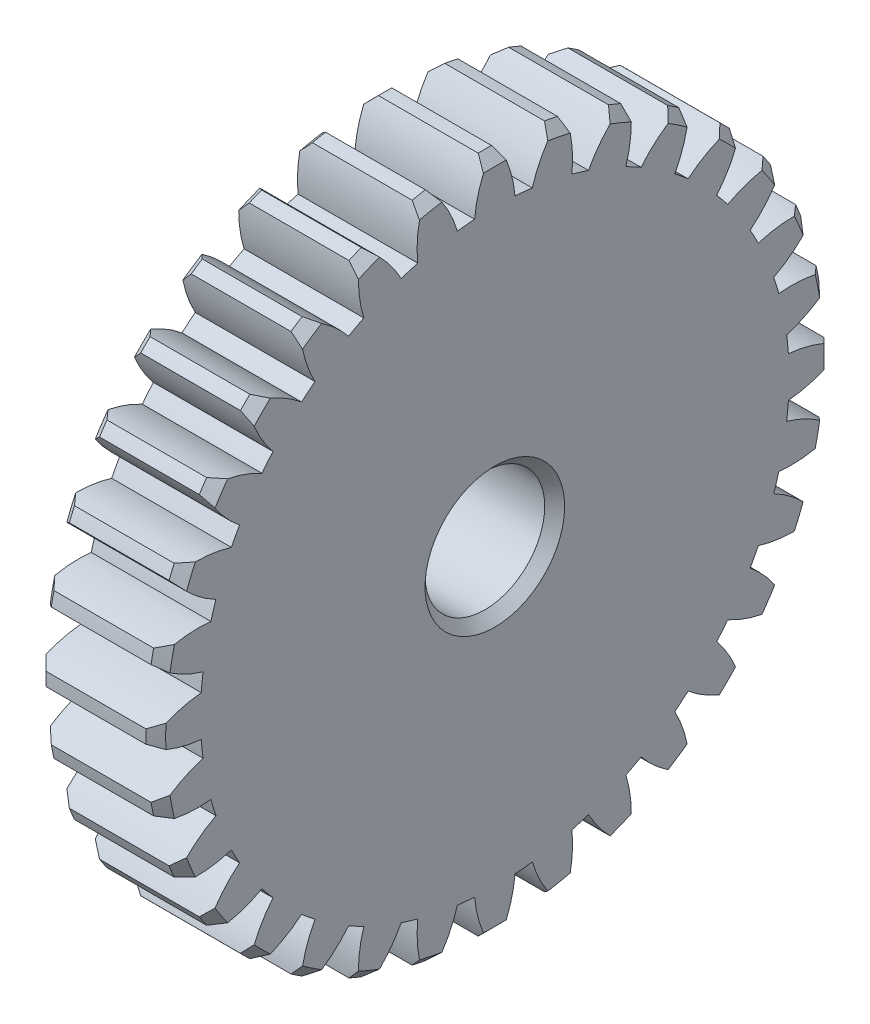
SolidWorks part; units mm, degrees
ref_plane "Front Plane" through (0, 0, 0) normal (0, 0, 1) x (1, 0, 0)
ref_plane "Top Plane" through (0, 0, 0) normal (0, 1, 0) x (1, 0, 0)
ref_plane "Right Plane" through (0, 0, 0) normal (1, 0, 0) x (0, 0, -1)
sketch "Sketch1" plane through (0, 0, 0) normal (0, 0, 1) x (1, 0, 0)
  line L0 (0, 17) -> (0, 0)
  line L1 (0, 0) -> (6, 0)
  line L2 (6, 0) -> (6, 17)
  line L3 (6, 17) -> (0, 17)
  line L4 (0, 0) -> (6, 0) construction
revolve "Revolve1" add sketch "Sketch1" angle 360 about L4
sketch "Sketch2" plane through (6, 0, 0) normal (1, 0, 0) x (0, 0, -1)
  arc A0 (2.9885, 16.7353) -> (0.3338, 16.9967) centre (0, 0) ccw
  arc A1 (0.3338, 16.9967) -> (1.0129, 14.7152) centre (-4.9631, 14.1783) cw
  arc A2 (1.0129, 14.7152) -> (1.8774, 14.63) centre (0, 0) cw
  arc A3 (1.8774, 14.63) -> (2.9885, 16.7353) centre (7.6338, 12.9376) cw
extrude "Cut-Extrude1" cut sketch "Sketch2" against normal through all
sketch "Sketch3" plane through (6, 0, 0) normal (1, 0, 0) x (0, 0, -1)
  arc A0 (6.196, 15.8307) -> (3.6433, 16.605) centre (0, 0) ccw
  arc A1 (3.6433, 16.605) -> (3.8642, 14.2348) centre (-2.1017, 14.8741) cw
  arc A2 (3.8642, 14.2348) -> (4.6955, 13.9827) centre (0, 0) cw
  arc A3 (4.6955, 13.9827) -> (6.196, 15.8307) centre (10.0111, 11.1998) cw
extrude "Cut-Extrude2" cut sketch "Sketch3" against normal through all
sketch "Sketch4" plane through (6, 0, 0) normal (1, 0, 0) x (0, 0, -1)
  arc A0 (9.1654, 14.3177) -> (6.8127, 15.5752) centre (0, 0) ccw
  arc A1 (6.8127, 15.5752) -> (6.567, 13.2075) centre (0.8405, 14.9983) cw
  arc A2 (6.567, 13.2075) -> (7.3332, 12.7979) centre (0, 0) cw
  arc A3 (7.3332, 12.7979) -> (9.1654, 14.3177) centre (12.0037, 9.0315) cw
extrude "Cut-Extrude3" cut sketch "Sketch4" against normal through all
sketch "Sketch5" plane through (6, 0, 0) normal (1, 0, 0) x (0, 0, -1)
  arc A0 (11.7825, 12.2545) -> (9.7204, 13.9468) centre (0, 0) ccw
  arc A1 (9.7204, 13.9468) -> (9.0175, 11.6725) centre (3.7504, 14.5462) cw
  arc A2 (9.0175, 11.6725) -> (9.689, 11.1214) centre (0, 0) cw
  arc A3 (9.689, 11.1214) -> (11.7825, 12.2545) centre (13.535, 6.5162) cw
extrude "Cut-Extrude4" cut sketch "Sketch5" against normal through all
sketch "Sketch6" plane through (6, 0, 0) normal (1, 0, 0) x (0, 0, -1)
  arc A0 (13.9468, 9.7204) -> (12.2545, 11.7825) centre (0, 0) ccw
  arc A1 (12.2545, 11.7825) -> (11.1214, 9.689) centre (6.5162, 13.535) cw
  arc A2 (11.1214, 9.689) -> (11.6725, 9.0175) centre (0, 0) cw
  arc A3 (11.6725, 9.0175) -> (13.9468, 9.7204) centre (14.5462, 3.7504) cw
extrude "Cut-Extrude5" cut sketch "Sketch6" against normal through all
sketch "Sketch7" plane through (6, 0, 0) normal (1, 0, 0) x (0, 0, -1)
  arc A0 (15.5752, 6.8127) -> (14.3177, 9.1654) centre (0, 0) ccw
  arc A1 (14.3177, 9.1654) -> (12.7979, 7.3332) centre (9.0315, 12.0037) cw
  arc A2 (12.7979, 7.3332) -> (13.2075, 6.567) centre (0, 0) cw
  arc A3 (13.2075, 6.567) -> (15.5752, 6.8127) centre (14.9983, 0.8405) cw
extrude "Cut-Extrude6" cut sketch "Sketch7" against normal through all
sketch "Sketch8" plane through (6, 0, 0) normal (1, 0, 0) x (0, 0, -1)
  arc A0 (16.605, 3.6433) -> (15.8307, 6.196) centre (0, 0) ccw
  arc A1 (15.8307, 6.196) -> (13.9827, 4.6955) centre (11.1998, 10.0111) cw
  arc A2 (13.9827, 4.6955) -> (14.2348, 3.8642) centre (0, 0) cw
  arc A3 (14.2348, 3.8642) -> (16.605, 3.6433) centre (14.8741, -2.1017) cw
extrude "Cut-Extrude7" cut sketch "Sketch8" against normal through all
sketch "Sketch9" plane through (6, 0, 0) normal (1, 0, 0) x (0, 0, -1)
  arc A0 (16.9967, 0.3338) -> (16.7353, 2.9885) centre (0, 0) ccw
  arc A1 (16.7353, 2.9885) -> (14.63, 1.8774) centre (12.9376, 7.6338) cw
  arc A2 (14.63, 1.8774) -> (14.7152, 1.0129) centre (0, 0) cw
  arc A3 (14.7152, 1.0129) -> (16.9967, 0.3338) centre (14.1783, -4.9631) cw
extrude "Cut-Extrude8" cut sketch "Sketch9" against normal through all
sketch "Sketch10" plane through (6, 0, 0) normal (1, 0, 0) x (0, 0, -1)
  arc A0 (16.7353, -2.9885) -> (16.9967, -0.3338) centre (0, 0) ccw
  arc A1 (16.9967, -0.3338) -> (14.7152, -1.0129) centre (14.1783, 4.9631) cw
  arc A2 (14.7152, -1.0129) -> (14.63, -1.8774) centre (0, 0) cw
  arc A3 (14.63, -1.8774) -> (16.7353, -2.9885) centre (12.9376, -7.6338) cw
extrude "Cut-Extrude9" cut sketch "Sketch10" against normal through all
sketch "Sketch11" plane through (6, 0, 0) normal (1, 0, 0) x (0, 0, -1)
  arc A0 (15.8307, -6.196) -> (16.605, -3.6433) centre (0, 0) ccw
  arc A1 (16.605, -3.6433) -> (14.2348, -3.8642) centre (14.8741, 2.1017) cw
  arc A2 (14.2348, -3.8642) -> (13.9827, -4.6955) centre (0, 0) cw
  arc A3 (13.9827, -4.6955) -> (15.8307, -6.196) centre (11.1998, -10.0111) cw
extrude "Cut-Extrude10" cut sketch "Sketch11" against normal through all
sketch "Sketch12" plane through (6, 0, 0) normal (1, 0, 0) x (0, 0, -1)
  arc A0 (14.3177, -9.1654) -> (15.5752, -6.8127) centre (0, 0) ccw
  arc A1 (15.5752, -6.8127) -> (13.2075, -6.567) centre (14.9983, -0.8405) cw
  arc A2 (13.2075, -6.567) -> (12.7979, -7.3332) centre (0, 0) cw
  arc A3 (12.7979, -7.3332) -> (14.3177, -9.1654) centre (9.0315, -12.0037) cw
extrude "Cut-Extrude11" cut sketch "Sketch12" against normal through all
sketch "Sketch13" plane through (6, 0, 0) normal (1, 0, 0) x (0, 0, -1)
  arc A0 (12.2545, -11.7825) -> (13.9468, -9.7204) centre (0, 0) ccw
  arc A1 (13.9468, -9.7204) -> (11.6725, -9.0175) centre (14.5462, -3.7504) cw
  arc A2 (11.6725, -9.0175) -> (11.1214, -9.689) centre (0, 0) cw
  arc A3 (11.1214, -9.689) -> (12.2545, -11.7825) centre (6.5162, -13.535) cw
extrude "Cut-Extrude12" cut sketch "Sketch13" against normal through all
sketch "Sketch14" plane through (6, 0, 0) normal (1, 0, 0) x (0, 0, -1)
  arc A0 (9.7204, -13.9468) -> (11.7825, -12.2545) centre (0, 0) ccw
  arc A1 (11.7825, -12.2545) -> (9.689, -11.1214) centre (13.535, -6.5162) cw
  arc A2 (9.689, -11.1214) -> (9.0175, -11.6725) centre (0, 0) cw
  arc A3 (9.0175, -11.6725) -> (9.7204, -13.9468) centre (3.7504, -14.5462) cw
extrude "Cut-Extrude13" cut sketch "Sketch14" against normal through all
sketch "Sketch15" plane through (6, 0, 0) normal (1, 0, 0) x (0, 0, -1)
  arc A0 (6.8127, -15.5752) -> (9.1654, -14.3177) centre (0, 0) ccw
  arc A1 (9.1654, -14.3177) -> (7.3332, -12.7979) centre (12.0037, -9.0315) cw
  arc A2 (7.3332, -12.7979) -> (6.567, -13.2075) centre (0, 0) cw
  arc A3 (6.567, -13.2075) -> (6.8127, -15.5752) centre (0.8405, -14.9983) cw
extrude "Cut-Extrude14" cut sketch "Sketch15" against normal through all
sketch "Sketch16" plane through (6, 0, 0) normal (1, 0, 0) x (0, 0, -1)
  arc A0 (3.6433, -16.605) -> (6.196, -15.8307) centre (0, 0) ccw
  arc A1 (6.196, -15.8307) -> (4.6955, -13.9827) centre (10.0111, -11.1998) cw
  arc A2 (4.6955, -13.9827) -> (3.8642, -14.2348) centre (0, 0) cw
  arc A3 (3.8642, -14.2348) -> (3.6433, -16.605) centre (-2.1017, -14.8741) cw
extrude "Cut-Extrude15" cut sketch "Sketch16" against normal through all
sketch "Sketch17" plane through (6, 0, 0) normal (1, 0, 0) x (0, 0, -1)
  arc A0 (0.3338, -16.9967) -> (2.9885, -16.7353) centre (0, 0) ccw
  arc A1 (2.9885, -16.7353) -> (1.8774, -14.63) centre (7.6338, -12.9376) cw
  arc A2 (1.8774, -14.63) -> (1.0129, -14.7152) centre (0, 0) cw
  arc A3 (1.0129, -14.7152) -> (0.3338, -16.9967) centre (-4.9631, -14.1783) cw
extrude "Cut-Extrude16" cut sketch "Sketch17" against normal through all
sketch "Sketch18" plane through (6, 0, 0) normal (1, 0, 0) x (0, 0, -1)
  arc A0 (-2.9885, -16.7353) -> (-0.3338, -16.9967) centre (0, 0) ccw
  arc A1 (-0.3338, -16.9967) -> (-1.0129, -14.7152) centre (4.9631, -14.1783) cw
  arc A2 (-1.0129, -14.7152) -> (-1.8774, -14.63) centre (0, 0) cw
  arc A3 (-1.8774, -14.63) -> (-2.9885, -16.7353) centre (-7.6338, -12.9376) cw
extrude "Cut-Extrude17" cut sketch "Sketch18" against normal through all
sketch "Sketch19" plane through (6, 0, 0) normal (1, 0, 0) x (0, 0, -1)
  arc A0 (-6.196, -15.8307) -> (-3.6433, -16.605) centre (0, 0) ccw
  arc A1 (-3.6433, -16.605) -> (-3.8642, -14.2348) centre (2.1017, -14.8741) cw
  arc A2 (-3.8642, -14.2348) -> (-4.6955, -13.9827) centre (0, 0) cw
  arc A3 (-4.6955, -13.9827) -> (-6.196, -15.8307) centre (-10.0111, -11.1998) cw
extrude "Cut-Extrude18" cut sketch "Sketch19" against normal through all
sketch "Sketch20" plane through (6, 0, 0) normal (1, 0, 0) x (0, 0, -1)
  arc A0 (-9.1654, -14.3177) -> (-6.8127, -15.5752) centre (0, 0) ccw
  arc A1 (-6.8127, -15.5752) -> (-6.567, -13.2075) centre (-0.8405, -14.9983) cw
  arc A2 (-6.567, -13.2075) -> (-7.3332, -12.7979) centre (0, 0) cw
  arc A3 (-7.3332, -12.7979) -> (-9.1654, -14.3177) centre (-12.0037, -9.0315) cw
extrude "Cut-Extrude19" cut sketch "Sketch20" against normal through all
sketch "Sketch21" plane through (6, 0, 0) normal (1, 0, 0) x (0, 0, -1)
  arc A0 (-11.7825, -12.2545) -> (-9.7204, -13.9468) centre (0, 0) ccw
  arc A1 (-9.7204, -13.9468) -> (-9.0175, -11.6725) centre (-3.7504, -14.5462) cw
  arc A2 (-9.0175, -11.6725) -> (-9.689, -11.1214) centre (0, 0) cw
  arc A3 (-9.689, -11.1214) -> (-11.7825, -12.2545) centre (-13.535, -6.5162) cw
extrude "Cut-Extrude20" cut sketch "Sketch21" against normal through all
sketch "Sketch22" plane through (6, 0, 0) normal (1, 0, 0) x (0, 0, -1)
  arc A0 (-13.9468, -9.7204) -> (-12.2545, -11.7825) centre (0, 0) ccw
  arc A1 (-12.2545, -11.7825) -> (-11.1214, -9.689) centre (-6.5162, -13.535) cw
  arc A2 (-11.1214, -9.689) -> (-11.6725, -9.0175) centre (0, 0) cw
  arc A3 (-11.6725, -9.0175) -> (-13.9468, -9.7204) centre (-14.5462, -3.7504) cw
extrude "Cut-Extrude21" cut sketch "Sketch22" against normal through all
sketch "Sketch23" plane through (6, 0, 0) normal (1, 0, 0) x (0, 0, -1)
  arc A0 (-15.5752, -6.8127) -> (-14.3177, -9.1654) centre (0, 0) ccw
  arc A1 (-14.3177, -9.1654) -> (-12.7979, -7.3332) centre (-9.0315, -12.0037) cw
  arc A2 (-12.7979, -7.3332) -> (-13.2075, -6.567) centre (0, 0) cw
  arc A3 (-13.2075, -6.567) -> (-15.5752, -6.8127) centre (-14.9983, -0.8405) cw
extrude "Cut-Extrude22" cut sketch "Sketch23" against normal through all
sketch "Sketch24" plane through (6, 0, 0) normal (1, 0, 0) x (0, 0, -1)
  arc A0 (-16.605, -3.6433) -> (-15.8307, -6.196) centre (0, 0) ccw
  arc A1 (-15.8307, -6.196) -> (-13.9827, -4.6955) centre (-11.1998, -10.0111) cw
  arc A2 (-13.9827, -4.6955) -> (-14.2348, -3.8642) centre (0, 0) cw
  arc A3 (-14.2348, -3.8642) -> (-16.605, -3.6433) centre (-14.8741, 2.1017) cw
extrude "Cut-Extrude23" cut sketch "Sketch24" against normal through all
sketch "Sketch25" plane through (6, 0, 0) normal (1, 0, 0) x (0, 0, -1)
  arc A0 (-16.9967, -0.3338) -> (-16.7353, -2.9885) centre (0, 0) ccw
  arc A1 (-16.7353, -2.9885) -> (-14.63, -1.8774) centre (-12.9376, -7.6338) cw
  arc A2 (-14.63, -1.8774) -> (-14.7152, -1.0129) centre (0, 0) cw
  arc A3 (-14.7152, -1.0129) -> (-16.9967, -0.3338) centre (-14.1783, 4.9631) cw
extrude "Cut-Extrude24" cut sketch "Sketch25" against normal through all
sketch "Sketch26" plane through (6, 0, 0) normal (1, 0, 0) x (0, 0, -1)
  arc A0 (-16.7353, 2.9885) -> (-16.9967, 0.3338) centre (0, 0) ccw
  arc A1 (-16.9967, 0.3338) -> (-14.7152, 1.0129) centre (-14.1783, -4.9631) cw
  arc A2 (-14.7152, 1.0129) -> (-14.63, 1.8774) centre (0, 0) cw
  arc A3 (-14.63, 1.8774) -> (-16.7353, 2.9885) centre (-12.9376, 7.6338) cw
extrude "Cut-Extrude25" cut sketch "Sketch26" against normal through all
sketch "Sketch27" plane through (6, 0, 0) normal (1, 0, 0) x (0, 0, -1)
  arc A0 (-15.8307, 6.196) -> (-16.605, 3.6433) centre (0, 0) ccw
  arc A1 (-16.605, 3.6433) -> (-14.2348, 3.8642) centre (-14.8741, -2.1017) cw
  arc A2 (-14.2348, 3.8642) -> (-13.9827, 4.6955) centre (0, 0) cw
  arc A3 (-13.9827, 4.6955) -> (-15.8307, 6.196) centre (-11.1998, 10.0111) cw
extrude "Cut-Extrude26" cut sketch "Sketch27" against normal through all
sketch "Sketch28" plane through (6, 0, 0) normal (1, 0, 0) x (0, 0, -1)
  arc A0 (-14.3177, 9.1654) -> (-15.5752, 6.8127) centre (0, 0) ccw
  arc A1 (-15.5752, 6.8127) -> (-13.2075, 6.567) centre (-14.9983, 0.8405) cw
  arc A2 (-13.2075, 6.567) -> (-12.7979, 7.3332) centre (0, 0) cw
  arc A3 (-12.7979, 7.3332) -> (-14.3177, 9.1654) centre (-9.0315, 12.0037) cw
extrude "Cut-Extrude27" cut sketch "Sketch28" against normal through all
sketch "Sketch29" plane through (6, 0, 0) normal (1, 0, 0) x (0, 0, -1)
  arc A0 (-12.2545, 11.7825) -> (-13.9468, 9.7204) centre (0, 0) ccw
  arc A1 (-13.9468, 9.7204) -> (-11.6725, 9.0175) centre (-14.5462, 3.7504) cw
  arc A2 (-11.6725, 9.0175) -> (-11.1214, 9.689) centre (0, 0) cw
  arc A3 (-11.1214, 9.689) -> (-12.2545, 11.7825) centre (-6.5162, 13.535) cw
extrude "Cut-Extrude28" cut sketch "Sketch29" against normal through all
sketch "Sketch30" plane through (6, 0, 0) normal (1, 0, 0) x (0, 0, -1)
  arc A0 (-9.7204, 13.9468) -> (-11.7825, 12.2545) centre (0, 0) ccw
  arc A1 (-11.7825, 12.2545) -> (-9.689, 11.1214) centre (-13.535, 6.5162) cw
  arc A2 (-9.689, 11.1214) -> (-9.0175, 11.6725) centre (0, 0) cw
  arc A3 (-9.0175, 11.6725) -> (-9.7204, 13.9468) centre (-3.7504, 14.5462) cw
extrude "Cut-Extrude29" cut sketch "Sketch30" against normal through all
sketch "Sketch31" plane through (6, 0, 0) normal (1, 0, 0) x (0, 0, -1)
  arc A0 (-6.8127, 15.5752) -> (-9.1654, 14.3177) centre (0, 0) ccw
  arc A1 (-9.1654, 14.3177) -> (-7.3332, 12.7979) centre (-12.0037, 9.0315) cw
  arc A2 (-7.3332, 12.7979) -> (-6.567, 13.2075) centre (0, 0) cw
  arc A3 (-6.567, 13.2075) -> (-6.8127, 15.5752) centre (-0.8405, 14.9983) cw
extrude "Cut-Extrude30" cut sketch "Sketch31" against normal through all
sketch "Sketch32" plane through (6, 0, 0) normal (1, 0, 0) x (0, 0, -1)
  arc A0 (-3.6433, 16.605) -> (-6.196, 15.8307) centre (0, 0) ccw
  arc A1 (-6.196, 15.8307) -> (-4.6955, 13.9827) centre (-10.0111, 11.1998) cw
  arc A2 (-4.6955, 13.9827) -> (-3.8642, 14.2348) centre (0, 0) cw
  arc A3 (-3.8642, 14.2348) -> (-3.6433, 16.605) centre (2.1017, 14.8741) cw
extrude "Cut-Extrude31" cut sketch "Sketch32" against normal through all
sketch "Sketch33" plane through (6, 0, 0) normal (1, 0, 0) x (0, 0, -1)
  arc A0 (-0.3338, 16.9967) -> (-2.9885, 16.7353) centre (0, 0) ccw
  arc A1 (-2.9885, 16.7353) -> (-1.8774, 14.63) centre (-7.6338, 12.9376) cw
  arc A2 (-1.8774, 14.63) -> (-1.0129, 14.7152) centre (0, 0) cw
  arc A3 (-1.0129, 14.7152) -> (-0.3338, 16.9967) centre (4.9631, 14.1783) cw
extrude "Cut-Extrude32" cut sketch "Sketch33" against normal through all
hole_wizard "Ø6.0 (6) Diameter Hole1" positions "Sketch35" profile "Sketch34" hole size "Ø6.0" standard "ANSI Metric"
sketch "Sketch35" plane through (0, 0, 0) normal (-1, 0, 0) x (0, 0, 1)
  point P0 (0, 0)
sketch "Sketch34" plane through (0, 0, 0) normal (0, 1, 0) x (0, 0, 1)
  line L0 (0, 0) -> (0, 6)
  line L1 (0, 6) -> (3, 6)
  line L2 (3, 6) -> (3, 0)
  line L5 (3, 0) -> (0, 0)
  line L11 (0, -6.35) -> (0, 107.95) construction
  dimension "Thru Hole Dia." = 6
  dimension "Thru Hole Depth" = 6
chamfer "Chamfer1" distance 0.5 angle 45 66 edges at (0, 17, 0) (0, -3.3165, -16.6733) (0, 16.6733, -3.3165) (6, 3.3165, 16.6733) (0, -16.6733, 3.3165) (6, 6.5056, 15.706) (0, 12.0208, 12.0208) (6, 9.4447, 14.135) (0, 9.4447, -14.135) (6, 12.0208, 12.0208) (0, -14.135, -9.4447) (6, 14.135, 9.4447) (0, -9.4447, 14.135) (6, 15.706, 6.5056) (0, 6.5056, 15.706) (6, 16.6733, 3.3165) (0, 15.706, 6.5056) (6, 16.6733, -3.3165) (0, 14.135, -9.4447) (6, 15.706, -6.5056) (0, 3.3165, -16.6733) (6, 14.135, -9.4447) (0, -9.4447, -14.135) (6, 12.0208, -12.0208) (0, -16.6733, -3.3165) (6, 9.4447, -14.135) (0, -14.135, 9.4447) (6, 6.5056, -15.706) (0, -3.3165, 16.6733) (6, 3.3165, -16.6733) (6, 0, 3) (6, 0, -17) (0, 9.4447, 14.135) (6, -3.3165, -16.6733) (0, 14.135, 9.4447) (6, -6.5056, -15.706) (0, 16.6733, 3.3165) (6, -9.4447, -14.135) (0, 15.706, -6.5056) (6, -12.0208, -12.0208) (0, 12.0208, -12.0208) (6, -14.135, -9.4447) (0, 6.5056, -15.706) (6, -15.706, -6.5056) (0, 0, -17) (6, -16.6733, -3.3165) (0, -6.5056, -15.706) (6, -17, 0) (0, -12.0208, -12.0208) (6, -16.6733, 3.3165) (0, -15.706, -6.5056) (6, -15.706, 6.5056) (0, -17, 0) (6, -14.135, 9.4447) (0, -15.706, 6.5056) (6, -12.0208, 12.0208) (0, -12.0208, 12.0208) (6, -9.4447, 14.135) (0, -6.5056, 15.706) (6, -6.5056, 15.706) (6, 17, 0) (6, -3.3165, 16.6733) (0, 0, 3) (0, 0, 17) (6, 0, 17) (0, 3.3165, 16.6733)
